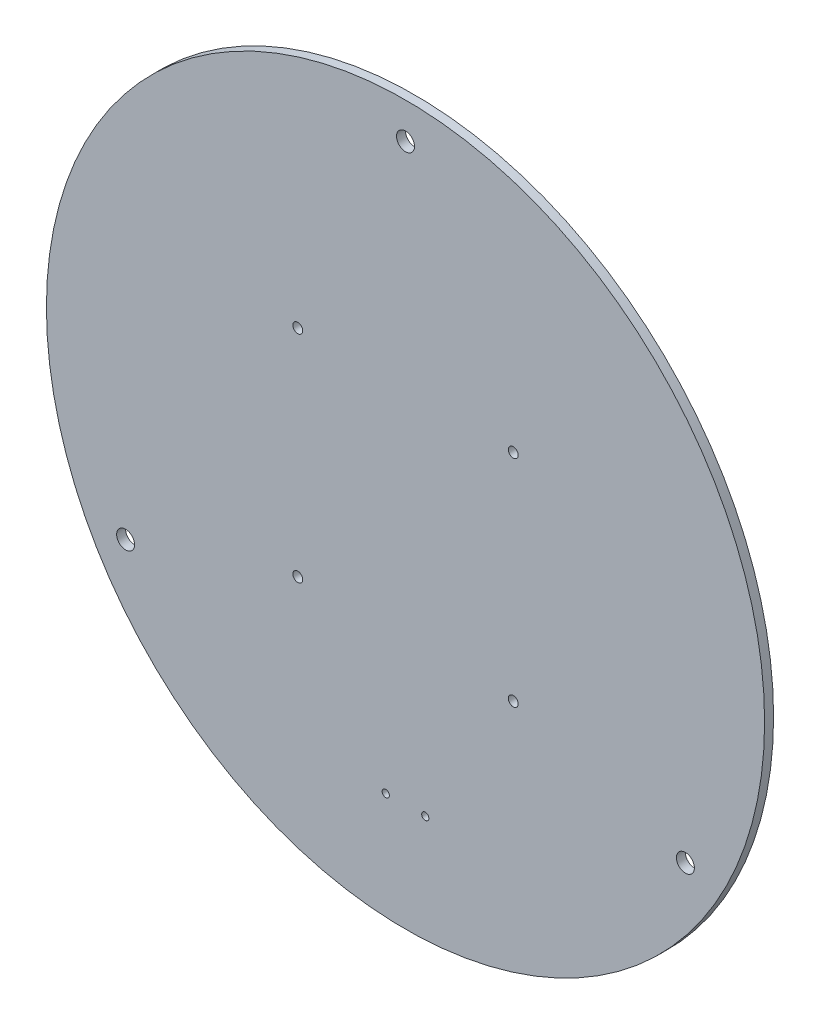
SolidWorks part; units mm, degrees
material "7075-T6 (SN)"
ref_plane "Front Plane" through (0, 0, 0) normal (0, 0, 1) x (1, 0, 0)
ref_plane "Top Plane" through (0, 0, 0) normal (0, 1, 0) x (1, 0, 0)
ref_plane "Right Plane" through (0, 0, 0) normal (1, 0, 0) x (0, 0, -1)
sketch "Sketch1" plane through (0, 0, 0) normal (0, 0, 1) x (1, 0, 0)
  circle A0 centre (0, 0) radius 200
  dimension "D1" = 400
extrude "Boss-Extrude1" add sketch "Sketch1" along normal blind 5
sketch "Sketch2" plane through (0, 0, 5) normal (0, 0, 1) x (1, 0, 0)
  line L0 (0, 0) -> (0, 238.8935) construction
  line L1 (0, 0) -> (306.4485, -176.9281) construction
  line L2 (0, 0) -> (-253.024, -146.0835) construction
  circle A0 centre (0, 0) radius 180 construction
  circle A1 centre (0, 0) radius 200 construction
  circle A2 centre (0, 180) radius 5
  circle A3 centre (155.8846, -90) radius 5
  circle A4 centre (-155.8846, -90) radius 5
  dimension "D1" = 20
  dimension "D4" = 10
  dimension "D5" = 10
  dimension "D6" = 10
  dimension "D2" = 120
  dimension "D3" = 120
extrude "Cut-Extrude1" cut sketch "Sketch2" against normal up to next
sketch "Sketch3" plane through (0, 0, 5) normal (0, 0, 1) x (1, 0, 0)
  line L1 (-60, -60) -> (60, -60) construction
  line L2 (-60, -60) -> (-60, 60) construction
  line L3 (-60, 60) -> (60, 60) construction
  line L4 (60, -60) -> (60, 60) construction
  line L5 (-60, -60) -> (60, 60) construction
  line L6 (-60, 60) -> (60, -60) construction
  circle A0 centre (-60, 60) radius 2.75
  circle A1 centre (60, 60) radius 2.75
  circle A2 centre (60, -60) radius 2.75
  circle A3 centre (-60, -60) radius 2.75
  point P0 (0, 0)
  dimension "D3" = 5.5
  dimension "D4" = 5.5
  dimension "D5" = 5.5
  dimension "D6" = 5.5
  dimension "D1" = 120
  dimension "D2" = 120
extrude "Cut-Extrude2" cut sketch "Sketch3" against normal up to next
sketch "Sketch4" plane through (0, 0, 5) normal (0, 0, 1) x (1, 0, 0)
  line L0 (0, 0) -> (0, -229.0198) construction
  line L1 (-11, -140) -> (11, -140) construction
  circle A0 centre (11, -140) radius 2
  circle A1 centre (-11, -140) radius 2
  point P6 (0, -140)
  dimension "D2" = 4
  dimension "D3" = 4
  dimension "D1" = 22
  dimension "D4" = 140
extrude "Cut-Extrude3" cut sketch "Sketch4" against normal up to next
